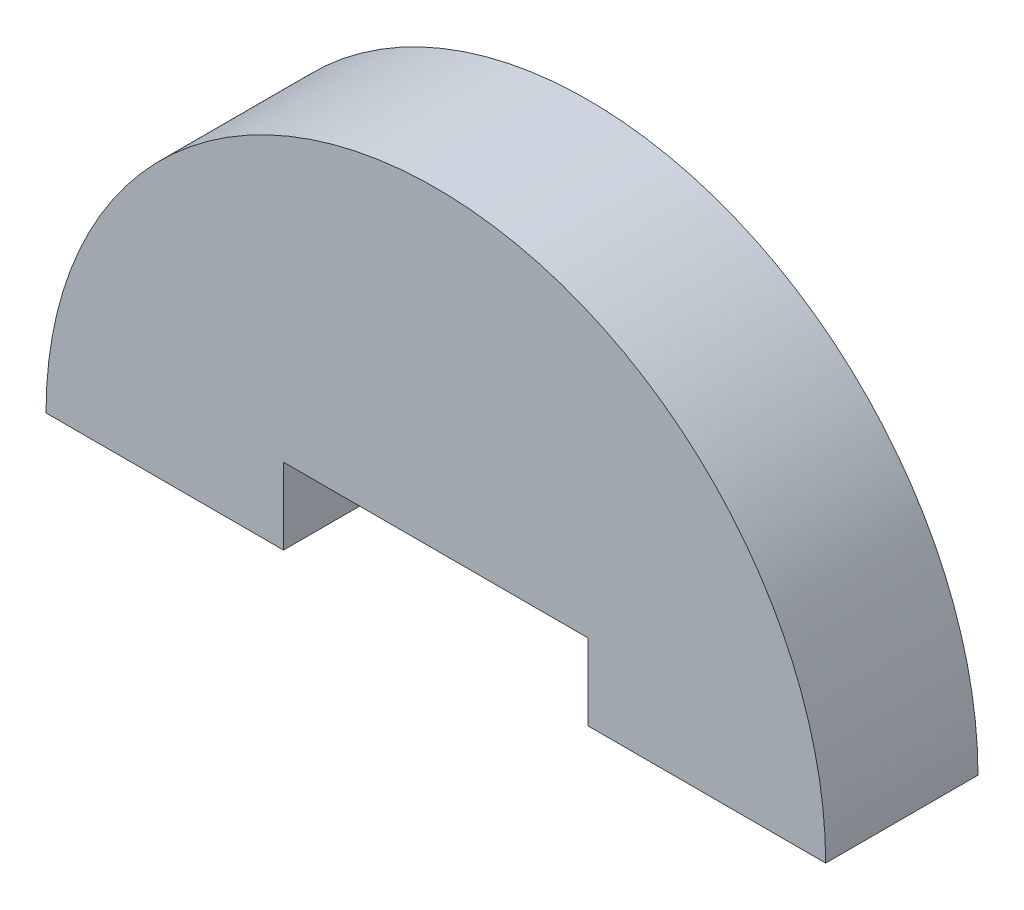
SolidWorks part; units mm, degrees
ref_plane "Front Plane" through (0, 0, 0) normal (0, 0, 1) x (1, 0, 0)
ref_plane "Top Plane" through (0, 0, 0) normal (0, 1, 0) x (1, 0, 0)
ref_plane "Right Plane" through (0, 0, 0) normal (1, 0, 0) x (0, 0, -1)
sketch "Model" plane through (0, 0, 0) normal (0, 0, 1) x (1, 0, 0)
  line L0 (3516.8656, 1303.5464) -> (3516.8656, 1300.5464)
  line L1 (3504.8656, 1303.5464) -> (3504.8656, 1300.5464)
  line L2 (3504.8656, 1303.5464) -> (3516.8656, 1303.5464)
  line L3 (3495.5084, 1300.5464) -> (3504.8656, 1300.5464)
  line L4 (3516.8656, 1300.5464) -> (3526.2227, 1300.5464)
  arc A0 (3526.2227, 1300.5464) -> (3495.5084, 1300.5464) centre (3510.8656, 1300.5464) ccw
extrude "Boss-Extrude1" add sketch "Model" along normal blind 6 contours A0 L3 L1 L2 L0 L4
